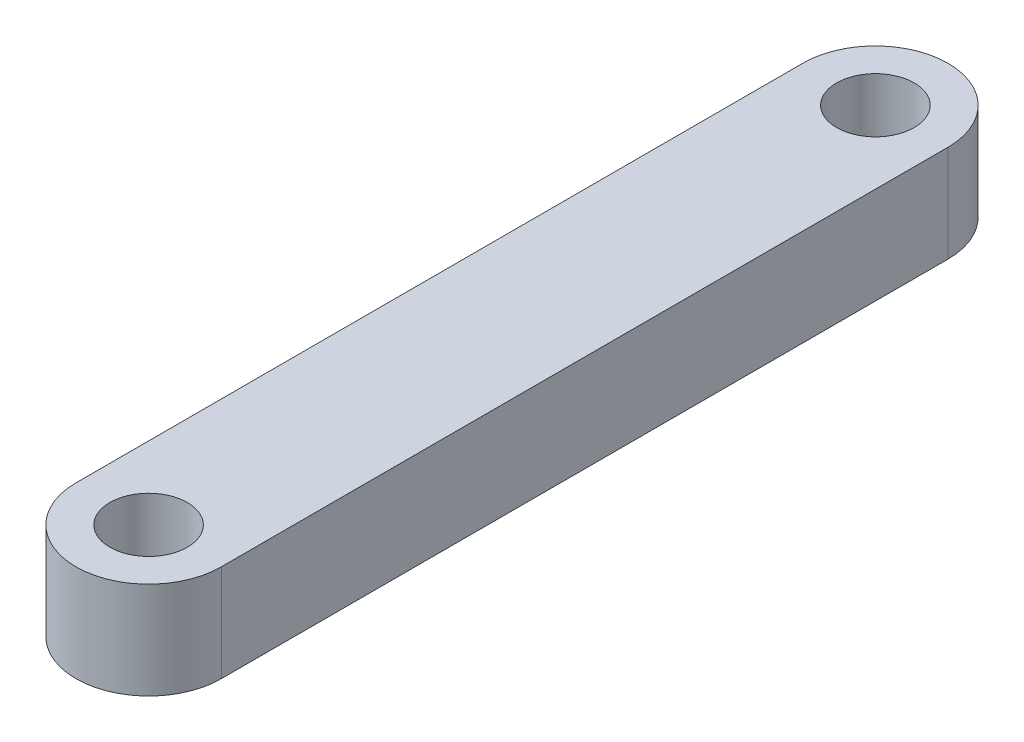
SolidWorks part; units mm, degrees
ref_plane "Front Plane" through (0, 0, 0) normal (0, 0, 1) x (1, 0, 0)
ref_plane "Top Plane" through (0, 0, 0) normal (0, 1, 0) x (1, 0, 0)
ref_plane "Right Plane" through (0, 0, 0) normal (1, 0, 0) x (0, 0, -1)
sketch "Sketch1" plane through (0, 0, 0) normal (0, 1, 0) x (1, 0, 0)
  line L0 (-1.5, 0) -> (1.5, 0) construction
  line L1 (-1.5, 7.5) -> (1.5, 7.5) construction
  line L2 (-1.5, 7.5) -> (-1.5, -7.5)
  line L3 (-1.5, -7.5) -> (1.5, -7.5) construction
  line L4 (1.5, 7.5) -> (1.5, -7.5)
  line L5 (-1.5, 7.5) -> (1.5, -7.5) construction
  line L6 (-1.5, -7.5) -> (1.5, 7.5) construction
  arc A0 (1.5, 7.5) -> (-1.5, 7.5) centre (0, 7.5) ccw
  arc A1 (1.5, -7.5) -> (-1.5, -7.5) centre (0, -7.5) cw
  circle A2 centre (0, 7.5) radius 0.8
  circle A3 centre (0, -7.5) radius 0.8
  point P0 (0, 0)
  dimension "D3" = 1.6
  dimension "D4" = 1.6
  dimension "D1" = 3
  dimension "D2" = 15
extrude "Boss-Extrude1" add sketch "Sketch1" along normal blind 2
